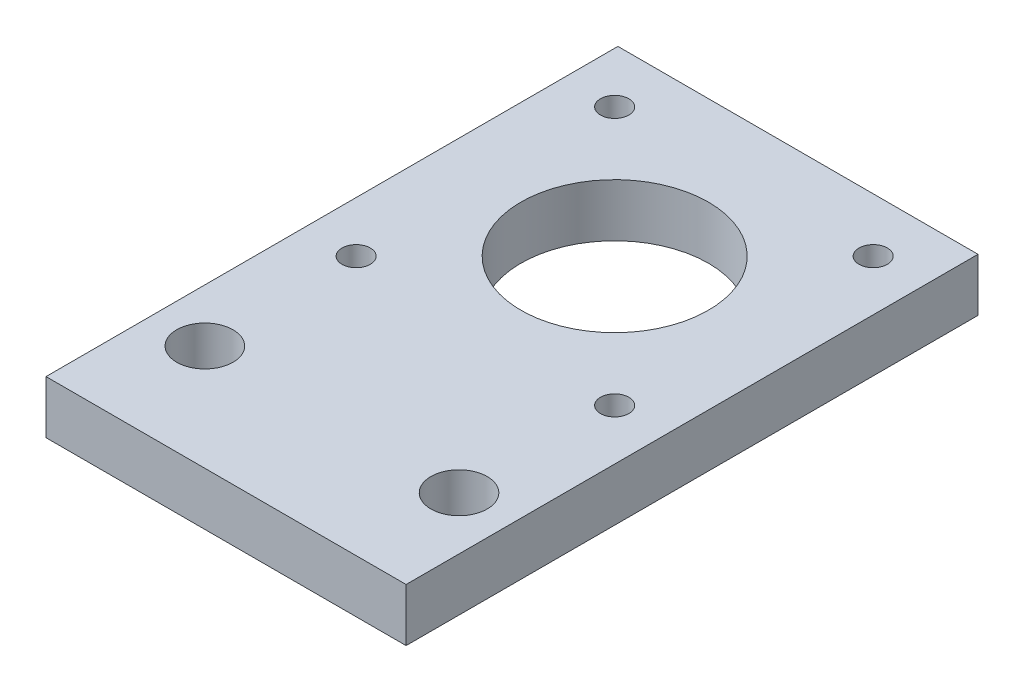
SolidWorks part; units mm, degrees
ref_plane "Front Plane" through (0, 0, 0) normal (0, 0, 1) x (1, 0, 0)
ref_plane "Top Plane" through (0, 0, 0) normal (0, 1, 0) x (1, 0, 0)
ref_plane "Right Plane" through (0, 0, 0) normal (1, 0, 0) x (0, 0, -1)
sketch "Sketch1" plane through (0, 0, 0) normal (0, 1, 0) x (1, 0, 0)
  line L1 (21.59, -34.29) -> (-21.59, -34.29)
  line L2 (21.59, -34.29) -> (21.59, 34.29)
  line L3 (21.59, 34.29) -> (-21.59, 34.29)
  line L4 (-21.59, -34.29) -> (-21.59, 34.29)
  line L5 (21.59, -34.29) -> (-21.59, 34.29) construction
  line L6 (21.59, 34.29) -> (-21.59, -34.29) construction
  point P0 (0, 0)
  dimension "D1" = 68.58
  dimension "D2" = 43.18
extrude "Boss-Extrude1" add sketch "Sketch1" along normal blind 6.35
ref_plane "Plane1" through (64.436, 9.2463, 34.29) normal (-1, 0, 0) x (0, 0, 1)
sketch "Sketch3" plane through (0, 0, 0) normal (0, -1, 0) x (1, 0, 0)
  line L0 (66.4507, 8.89) -> (-1152.7493, 8.89) construction
  line L1 (66.4507, 34.29) -> (-1152.7493, 34.29) construction
  line L2 (66.4507, 8.89) -> (-1152.7493, 8.89)
  line L3 (66.4507, 34.29) -> (-1152.7493, 34.29)
hole_wizard "1/4 Clearance Hole1" positions "Sketch4" profile "Sketch5" hole size "1/4" standard "ANSI Inch" end condition through all
sketch "Sketch4" plane through (0, 6.35, 0) normal (0, 1, 0) x (1, 0, 0)
  line L0 (-21.59, -8.89) -> (-21.59, -34.29) construction
  line L1 (66.4507, -8.89) -> (-1152.7493, -8.89) construction
  line L2 (-21.59, 34.29) -> (-21.59, -34.29) construction
  line L4 (-21.59, -21.59) -> (21.59, -21.59) construction
  line L5 (21.59, -34.29) -> (21.59, 34.29) construction
  point P15 (-15.24, -21.59)
  point P17 (15.24, -21.59)
  point P20 (0, -21.59)
  dimension "D1" = 15.24
  dimension "D2" = 15.24
sketch "Sketch5" plane through (15.24, 6.35, 21.59) normal (1, 0, 0) x (0, 0, 1)
  line L0 (0, 0) -> (0, 6.35)
  line L1 (0, 6.35) -> (3.3782, 6.35)
  line L2 (3.3782, 6.35) -> (3.3782, 0)
  line L5 (3.3782, 0) -> (0, 0)
  line L11 (0, -6.35) -> (0, 107.95) construction
  dimension "Thru Hole Dia." = 6.7564
  dimension "Thru Hole Depth" = 6.35
sketch "Sketch6" plane through (0, 0, 0) normal (0, -1, 0) x (1, 0, 0)
  circle A0 centre (0, -12.31) radius 10.985 construction
  circle A1 centre (15.5, 3.19) radius 2.155 construction
  circle A2 centre (-15.5, 3.19) radius 2.155 construction
  circle A3 centre (-15.5, -27.81) radius 2.155 construction
  circle A4 centre (15.5, -27.81) radius 2.155 construction
  circle A5 centre (0, -12.31) radius 10.985
  circle A6 centre (15.5, 3.19) radius 2.155
  circle A7 centre (-15.5, 3.19) radius 2.155
  circle A8 centre (-15.5, -27.81) radius 2.155
  circle A9 centre (15.5, -27.81) radius 2.155
sketch "Sketch7" plane through (0, 0, 0) normal (0, -1, 0) x (1, 0, 0)
  circle A0 centre (0, -12.31) radius 11.239
  circle A1 centre (0, -12.31) radius 10.985 construction
  dimension "D1" = 0.254
extrude "Cut-Extrude1" cut sketch "Sketch7" against normal through all
hole_wizard "M3 Clearance Hole1" positions "Sketch8" profile "Sketch9" hole size "M3" standard "ANSI Metric" end condition through all
sketch "Sketch8" plane through (0, 0, 0) normal (0, -1, 0) x (-1, 0, 0)
  point P0 (-15.5, 27.81)
  point P3 (15.5, 27.81)
  point P6 (15.5, -3.19)
  point P9 (-15.5, -3.19)
sketch "Sketch9" plane through (15.5, 0, -27.81) normal (1, 0, 0) x (0, 0, -1)
  line L0 (0, 0) -> (0, 6.35)
  line L1 (0, 6.35) -> (1.7, 6.35)
  line L2 (1.7, 6.35) -> (1.7, 0)
  line L5 (1.7, 0) -> (0, 0)
  line L11 (0, -6.35) -> (0, 107.95) construction
  dimension "Thru Hole Dia." = 3.4
  dimension "Thru Hole Depth" = 6.35
